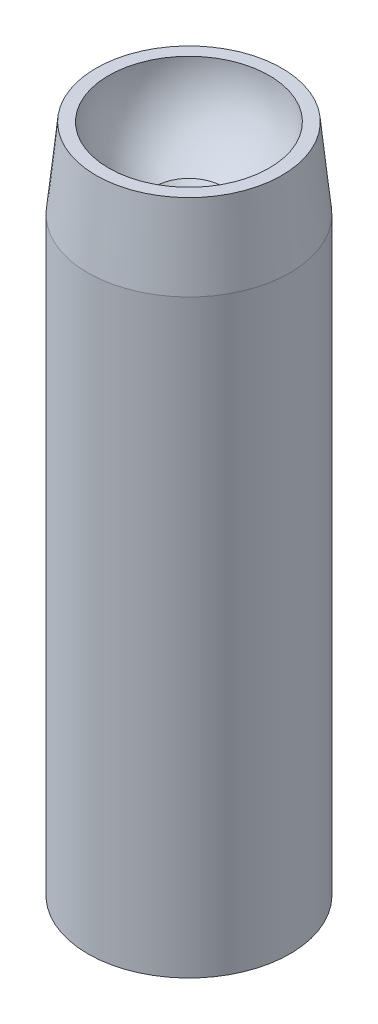
SolidWorks part; units mm, degrees
ref_plane "Front Plane" through (0, 0, 0) normal (0, 0, 1) x (1, 0, 0)
ref_plane "Top Plane" through (0, 0, 0) normal (0, 1, 0) x (1, 0, 0)
ref_plane "Right Plane" through (0, 0, 0) normal (1, 0, 0) x (0, 0, -1)
sketch "Sketch1" plane through (0, 0, 0) normal (0, 1, 0) x (1, 0, 0)
  circle A0 centre (0, 0) radius 5.2
  circle A1 centre (0, 0) radius 6
  dimension "D1" = 10.4
  dimension "D2" = 12
extrude "Boss-Extrude1" add sketch "Sketch1" along normal blind 25
sketch "Sketch2" plane through (0, 25, 0) normal (0, 1, 0) x (1, 0, 0)
  circle A0 centre (0, 0) radius 6
  circle A1 centre (0, 0) radius 5
  dimension "D1" = 10
extrude "Boss-Extrude2" add sketch "Sketch2" along normal blind 10
sketch "Sketch3" plane through (0, 0, 0) normal (1, 0, 0) x (0, 0, -1)
  line L0 (0, 33.9734) -> (0, -1.0266) construction
  line L1 (-6, 35) -> (-2, 35)
  line L2 (-2, 35.4403) -> (-1.5597, 35)
  line L3 (5, 35) -> (-5, 35) construction
  line L4 (0, 39.7625) -> (-5.5125, 39.7625) construction
  line L5 (-4.7625, 41.8018) -> (-4.7625, 37.7071) construction
  line L6 (-5.5125, 41.1922) -> (-5.5125, 38.3339) construction
  line L7 (-4.7625, 39.7625) -> (-5.5125, 39.7625)
  line L8 (-5.5125, 39.7625) -> (-6, 35)
  line L9 (6, 35) -> (-6, 35) construction
  line L10 (-2, 39.7625) -> (-2, 35) construction
  line L11 (-1.5597, 35) -> (-2, 35)
  arc A0 (-4.7625, 39.7625) -> (-2, 35.4403) centre (0, 39.7625) ccw
  dimension "D1" = 9.525
  dimension "D2" = 0.75
  dimension "D3" = 2
  dimension "D4" = 45
revolve "Revolve2" add sketch "Sketch3" angle 360 about L0
